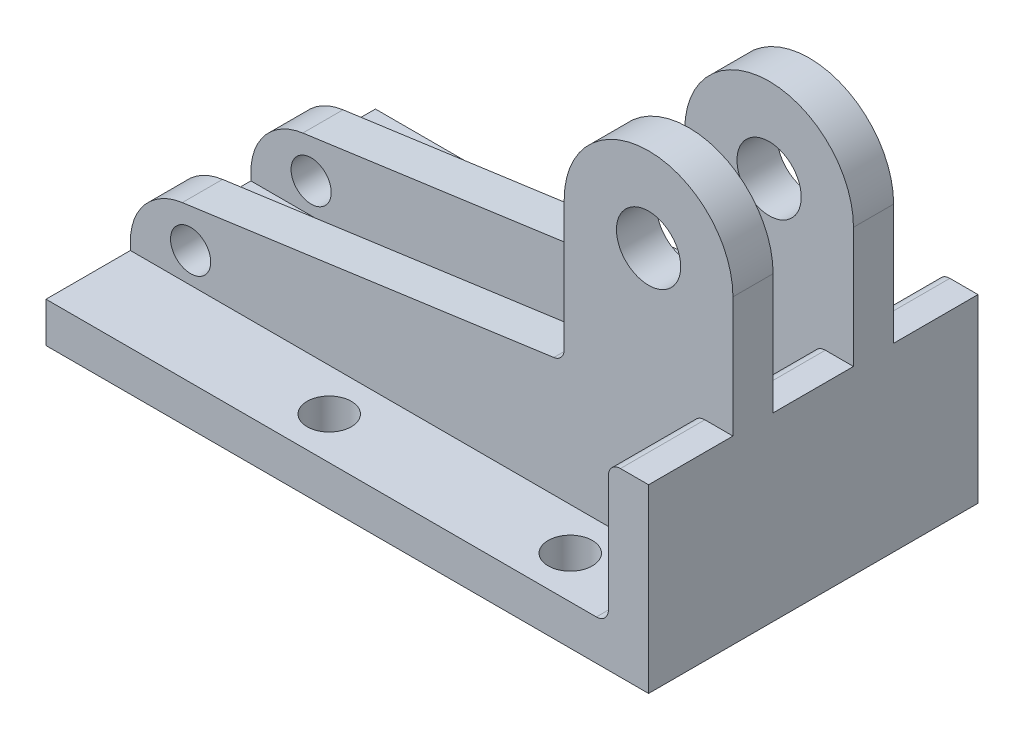
SolidWorks part; units mm, degrees
ref_plane "정면" through (0, 0, 0) normal (0, 0, 1) x (1, 0, 0)
ref_plane "윗면" through (0, 0, 0) normal (0, 1, 0) x (1, 0, 0)
ref_plane "우측면" through (0, 0, 0) normal (1, 0, 0) x (0, 0, -1)
sketch "스케치1" plane through (0, 0, 0) normal (0, 0, 1) x (1, 0, 0)
  line L0 (0, 0) -> (-150, 0)
  line L9 (-150, 0) -> (-150, 10)
  line L10 (-150, 10) -> (-10, 10)
  line L11 (-10, 10) -> (-10, 45)
  line L12 (-10, 45) -> (0, 45)
  line L13 (0, 45) -> (0, 0)
  dimension "D1" = 150
  dimension "D2" = 10
  dimension "D3" = 10
  dimension "D4" = 45
extrude "보스-돌출1" add sketch "스케치1" against normal blind 82
fillet "필렛1" radius 3 1 edges at (-10, 45, -41)
ref_plane "평면1" through (0, 0, -21) normal (0, 0, 1) x (1, 0, 0)
ref_plane "평면2" through (0, 0, -61) normal (0, 0, -1) x (-1, 0, 0)
sketch "스케치2" plane through (0, 0, -61) normal (0, 0, -1) x (-1, 0, 0)
  line L0 (150, 0) -> (150, 25)
  line L1 (150, 25) -> (42, 40)
  line L2 (42, 40) -> (42, 75)
  line L4 (0, 75) -> (0, 0)
  line L5 (0, 0) -> (150, 0)
  arc A0 (0, 75) -> (42, 75) centre (21, 75) cw
  dimension "D1" = 21
  dimension "D2" = 75
  dimension "D3" = 40
  dimension "D4" = 25
extrude "보스-돌출2" add sketch "스케치2" against normal blind 10
ref_plane "평면3" through (0, 0, -41) normal (0, 0, 1) x (1, 0, 0)
mirror "대칭 복사1" about plane through (0, 0, -41) normal (0, 0, 1) of "보스-돌출2"
sketch "스케치3" plane through (0, 0, -41) normal (0, 0, 1) x (1, 0, 0)
  line L0 (-150, 10) -> (-150, 25) construction
  line L1 (-10, 10) -> (-150, 10) construction
  circle A0 centre (-21, 75) radius 8
  arc A1 (0, 75) -> (-42, 75) centre (-21, 75) ccw construction
  circle A2 centre (-135, 17.5) radius 5
  point P7 (0, 0)
  dimension "D1" = 16
  dimension "D2" = 10
  dimension "D3" = 15
  dimension "D4" = 7.5
extrude "컷-돌출1" cut sketch "스케치3" against normal through all both and the other way through all
fillet "필렛2" radius 15 2 edges at (-150, 25, -26) (-150, 25, -56)
sketch "스케치4" plane through (0, 0, 0) normal (0, 1, 0) x (1, 0, 0)
  line L0 (0, 82) -> (0, 61) construction
  line L2 (-10, 82) -> (-150, 82) construction
  line L3 (-182.4405, 41) -> (39.7122, 41) construction
  line L5 (-24.75, 41) -> (24.75, 41) construction
  circle A0 centre (-30, 71.5) radius 5.5
  circle A1 centre (-90, 71.5) radius 5.5
  circle A2 centre (-30, 10.5) radius 5.5
  circle A3 centre (-90, 10.5) radius 5.5
  dimension "D1" = 11
  dimension "D4" = 11
  dimension "D2" = 30
  dimension "D3" = 10.5
  dimension "D5" = 60
extrude "컷-돌출2" cut sketch "스케치4" against normal through all and the other way through all
fillet "필렛3" radius 3 3 edges at (-10, 10, -41) (-10, 10, -71.5) (-10, 10, -10.5)
fillet "필렛4" radius 3 2 edges at (-42, 40, -26) (-42, 40, -56)
